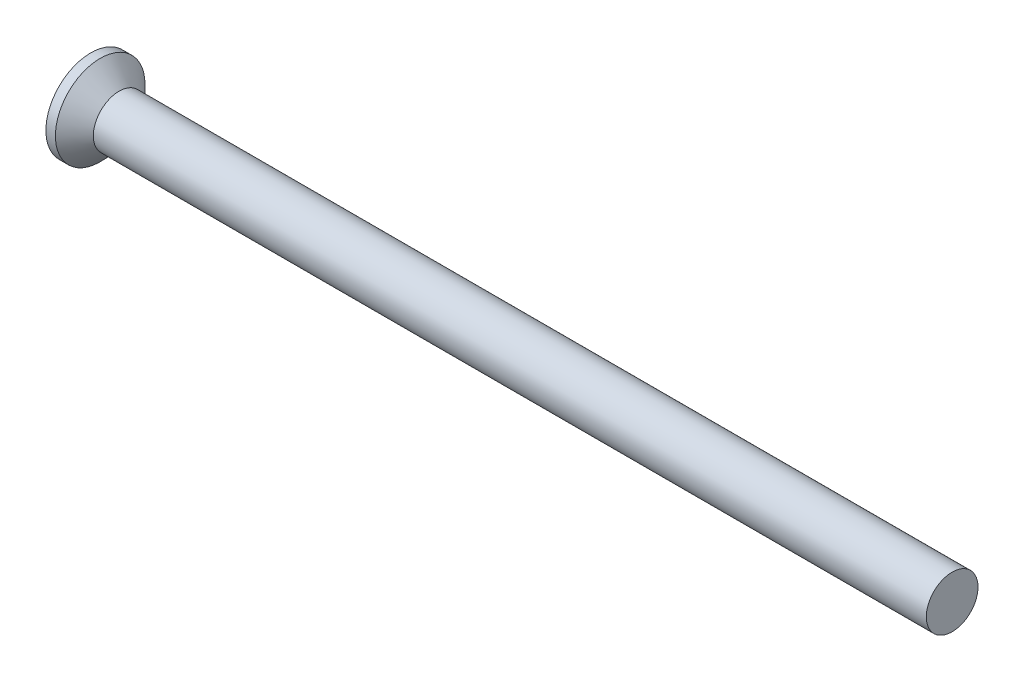
SolidWorks part; units mm, degrees
ref_plane "Front" through (0, 0, 0) normal (0, 0, 1) x (1, 0, 0)
ref_plane "Top" through (0, 0, 0) normal (0, 1, 0) x (1, 0, 0)
ref_plane "Right" through (0, 0, 0) normal (1, 0, 0) x (0, 0, -1)
sketch "Sketch1" plane through (0, 0, 0) normal (0, 0, 1) x (1, 0, 0)
  line L0 (50, 1.5) -> (2.65, 1.5)
  line L1 (2.65, 1.5) -> (1.65, 1.5)
  line L2 (1.65, 1.5) -> (0.55, 2.6)
  line L3 (0.55, 2.6) -> (0, 2.6)
  line L4 (50, 1.5) -> (50, 0)
  line L5 (4.5158, 0) -> (-89.8219, 0) construction
  line L6 (50, 0) -> (0, 0)
  line L7 (0, 2.6) -> (0, 0)
  dimension "d" = 3
  dimension "D1" = 45
  dimension "dk" = 5.2
  dimension "k" = 1.65
  dimension "l" = 50
  dimension "a" = 1
revolve "Base" add sketch "Sketch1" angle 360 about L5
cosmetic thread "ThreadCosmetic1" [suppressed] parameters "bb"=6.35, "THD_MINOR"=2.459
sketch "Sketch6" plane through (0, 0, 0) normal (1, 0, 0) x (0, 0, -1)
  line L0 (-1.9271, 0) -> (2.0512, 0) construction
  line L1 (0, 1.8651) -> (0, -2.0207) construction
  line L2 (0.32, 0.32) -> (0.32, 1.6)
  line L3 (0.32, 1.6) -> (-0.32, 1.6)
  line L4 (-0.32, 0.32) -> (-0.32, 1.6)
  line L5 (0.32, 0.32) -> (1.6, 0.32)
  line L6 (1.6, 0.32) -> (1.6, -0.32)
  line L7 (-1.6, 0.32) -> (-1.6, -0.32)
  line L8 (-0.32, 0.32) -> (-1.6, 0.32)
  line L9 (-0.32, -0.32) -> (-1.6, -0.32)
  line L10 (0.32, -0.32) -> (1.6, -0.32)
  line L11 (-0.32, -0.32) -> (-0.32, -1.6)
  line L12 (0.32, -1.6) -> (-0.32, -1.6)
  line L13 (0.32, -0.32) -> (0.32, -1.6)
  point P16 (-1.6, 0)
  point P17 (1.6, 0)
extrude "CrossRecess" cut sketch "Sketch6" along normal blind 0.825
draft "Draft9" type of draft neutral plane draft angle 30 faces to draft 4 face at (0.4125, -1.6, 0) face at (0.4125, 0, 1.6) face at (0.4125, 0, -1.6) face at (0.4125, 1.6, 0) neutral plane through (0, 2.6, 0) neutral plane normal (-1, 0, 0) parameters "D1"=30
fillet "Fillet5" radius 0.3 4 edges at (0.4125, -0.32, -0.32) (0.4125, -0.32, 0.32) (0.4125, 0.32, -0.32) (0.4125, 0.32, 0.32)
sketch "Sketch7" plane through (0, 0, 0) normal (1, 0, 0) x (0, 0, -1)
  line L0 (-2.0126, 0) -> (1.9757, 0) construction
  line L1 (0, 1.9314) -> (0, -2.0126) construction
  line L2 (0, 0) -> (1.5555, 1.5555) construction
  line L3 (0, 0.4782) -> (1.1314, 1.1314)
  line L4 (-1.5402, 1.5402) -> (0, 0) construction
  line L5 (0.4782, 0) -> (1.1314, 1.1314)
  line L6 (0, -0.4782) -> (1.1314, -1.1314)
  line L7 (0.4782, 0) -> (1.1314, -1.1314)
  line L8 (-0.4782, 0) -> (-1.1314, -1.1314)
  line L9 (0, -0.4782) -> (-1.1314, -1.1314)
  line L10 (-0.4782, 0) -> (-1.1314, 1.1314)
  line L11 (0, 0.4782) -> (-1.1314, 1.1314)
  dimension "D3" = 15
  dimension "m" = 3.2
extrude "Cut-Extrude3" [suppressed] cut sketch "Sketch7" along normal blind 10 draft 20
sketch "Sketch10" plane through (0, 0, 0) normal (0, 0, 1) x (1, 0, 0)
  line L0 (62.2289, 0) -> (-1.9277, 0) construction
  line L1 (1.65, 1.5) -> (2.15, 1.5)
  line L4 (2.15, 1.5) -> (2.15, 0)
  line L7 (2.15, 0) -> (1.65, 0)
  line L9 (1.65, 1.5) -> (0.55, 2.6) construction
  line L10 (1.65, 1.5) -> (1.65, 0)
  dimension "p" = 0.5
revolve "Revolve2" add sketch "Sketch10" angle 360 about L0
sketch "Sketch8" plane through (0, 0, 0) normal (0, 0, 1) x (1, 0, 0)
  line L0 (25, 1.5) -> (23.75, 1.2295)
  line L1 (23.75, 1.2295) -> (5, 1.2295)
  line L3 (50, -1.5) -> (50, 1.5) construction
  line L6 (5, 1.2295) -> (5, 6.2295)
  line L7 (5, 6.2295) -> (25, 6.2295)
  line L8 (25, 6.2295) -> (25, 1.5)
  line L9 (62.4753, 0) -> (52.9594, 0) construction
  dimension "D1" = 5
  dimension "x" = 1.25
  dimension "d" = 3
  dimension "THD_MINOR" = 2.459
  dimension "b" = 25
sketch "Sketch11" plane through (0, 0, 0) normal (0, 0, 1) x (1, 0, 0)
  line L0 (50, 1.2657) -> (50.1353, 1.5)
  line L1 (50.1353, 1.5) -> (50.1353, 1.7705)
  line L2 (50.1353, 1.7705) -> (49.8648, 1.7705)
  line L3 (49.8648, 1.7705) -> (49.8648, 1.5)
  line L4 (49.8648, 1.5) -> (50, 1.2657)
  line L5 (50, -1.5) -> (50, 1.5) construction
  line L6 (0, 0) -> (66.0064, 0) construction
  dimension "D1" = 3
  dimension "D2" = 0.2705
revolve "Cut-Revolve10" [suppressed] cut sketch "Sketch11" angle 360 about L6
pattern_linear "LPattern10" [suppressed] count 20 spacing 0.3246 along (1, 0, 0)
equation "\"D1@Sketch6\" = \"m@Sketch6\" / 5"
equation "\"D1@CrossRecess\" = \"k@Sketch1\" / 2"
equation "\"D1@Sketch11\" = \"d@Sketch1\""
equation "\"D2@Sketch11\" =  ( \"d@Sketch1\" - \"THD_MINOR@ThreadCosmetic1\" )  / 2"
equation "\"D3@LPattern10\" = \"D2@Sketch11\" * 1.2"
equation "\"D1@LPattern10\" = \"bb@ThreadCosmetic1\" / \"D3@LPattern10\" "
